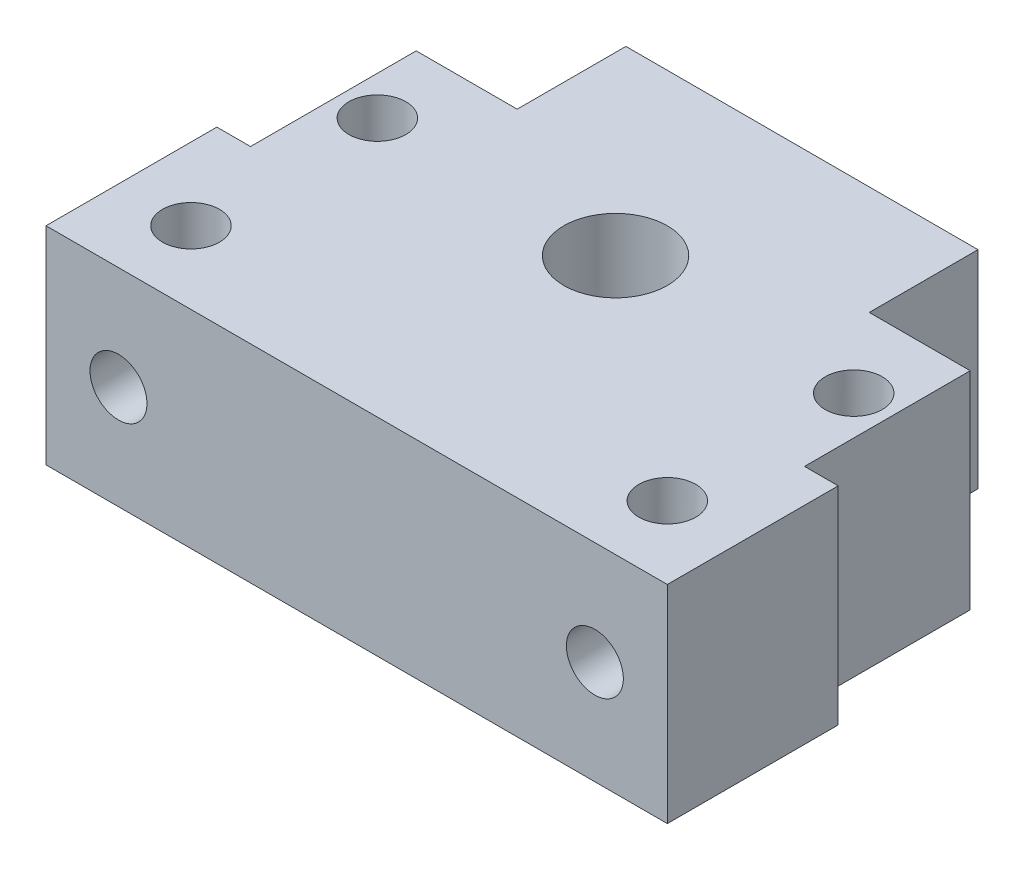
SolidWorks part; units mm, degrees
ref_plane "Front Plane" through (0, 0, 0) normal (0, 0, 1) x (1, 0, 0)
ref_plane "Top Plane" through (0, 0, 0) normal (0, 1, 0) x (1, 0, 0)
ref_plane "Right Plane" through (0, 0, 0) normal (1, 0, 0) x (0, 0, -1)
sketch "Sketch1" plane through (0, 0, 0) normal (0, 1, 0) x (1, 0, 0)
  line L0 (0, -21.5) -> (0, 21.5) construction
  line L1 (30, -21.5) -> (-30, -21.5)
  line L2 (30, -21.5) -> (30, 11)
  line L3 (17, 21.5) -> (-17, 21.5)
  line L4 (-30, -21.5) -> (-30, 11)
  line L5 (30, -21.5) -> (-17, 12.1833) construction
  line L6 (17, 12.1833) -> (-30, -21.5) construction
  line L9 (-30, 11) -> (-17, 11)
  line L10 (-17, 21.5) -> (-17, 11)
  line L15 (30, 11) -> (17, 11)
  line L16 (17, 21.5) -> (17, 11)
  line L20 (23, -14.5) -> (-23, -14.5) construction
  line L21 (23, -14.5) -> (23, 3.5) construction
  line L22 (23, 3.5) -> (-23, 3.5) construction
  line L23 (-23, -14.5) -> (-23, 3.5) construction
  line L24 (23, -14.5) -> (-23, 3.5) construction
  line L25 (23, 3.5) -> (-23, -14.5) construction
  circle A0 centre (0, 3.5) radius 5
  circle A1 centre (-23, 3.5) radius 2.75
  circle A2 centre (-23, -14.5) radius 2.75
  circle A3 centre (23, 3.5) radius 2.75
  circle A4 centre (23, -14.5) radius 2.75
  point P0 (0, 0)
  point P18 (0, -5.5)
  dimension "D8" = 10
  dimension "D9" = 5.5
  dimension "D1" = 34
  dimension "D2" = 60
  dimension "D3" = 43
  dimension "D4" = 32.5
  dimension "D5" = 32.5
  dimension "D6" = 25
  dimension "D7" = 30
  dimension "D10" = 46
  dimension "D11" = 18
  dimension "D12" = 0
extrude "Boss-Extrude1" add sketch "Sketch1" along normal blind 20
sketch "Sketch2" plane through (0, 0, -11) normal (0, 0, -1) x (-1, 0, 0)
  line L0 (30, 20) -> (30, 0) construction
  line L2 (-30, 20) -> (-30, 0) construction
  circle A0 centre (-23, 10) radius 2.75
  circle A1 centre (23, 10) radius 2.75
  dimension "D4" = 5.5
  dimension "D1" = 46
  dimension "D2" = 7
  dimension "D3" = 7
extrude "Cut-Extrude1" cut sketch "Sketch2" against normal through all
sketch "Sketch3" plane through (0, 0, 0) normal (0, -1, 0) x (1, 0, 0)
  line L1 (33.25, -27) -> (26.75, -27)
  line L2 (33.25, -27) -> (33.25, 5)
  line L3 (33.25, 5) -> (26.75, 5)
  line L4 (26.75, -27) -> (26.75, 5)
  line L5 (33.25, -27) -> (26.75, 5) construction
  line L6 (33.25, 5) -> (26.75, -27) construction
  line L7 (0, 21.5) -> (0, -43.7338) construction
  line L8 (-75, 21.5) -> (75, 21.5) construction
  line L9 (-33.25, 5) -> (-26.75, -27) construction
  line L10 (-33.25, -27) -> (-26.75, 5) construction
  line L11 (-26.75, -27) -> (-26.75, 5)
  line L12 (-33.25, 5) -> (-26.75, 5)
  line L13 (-33.25, -27) -> (-33.25, 5)
  line L14 (-33.25, -27) -> (-26.75, -27)
  point P0 (30, -11)
  point P18 (-30, -11)
  dimension "D1" = 32
  dimension "D2" = 6.5
extrude "Cut-Extrude2" cut sketch "Sketch3" against normal through all
